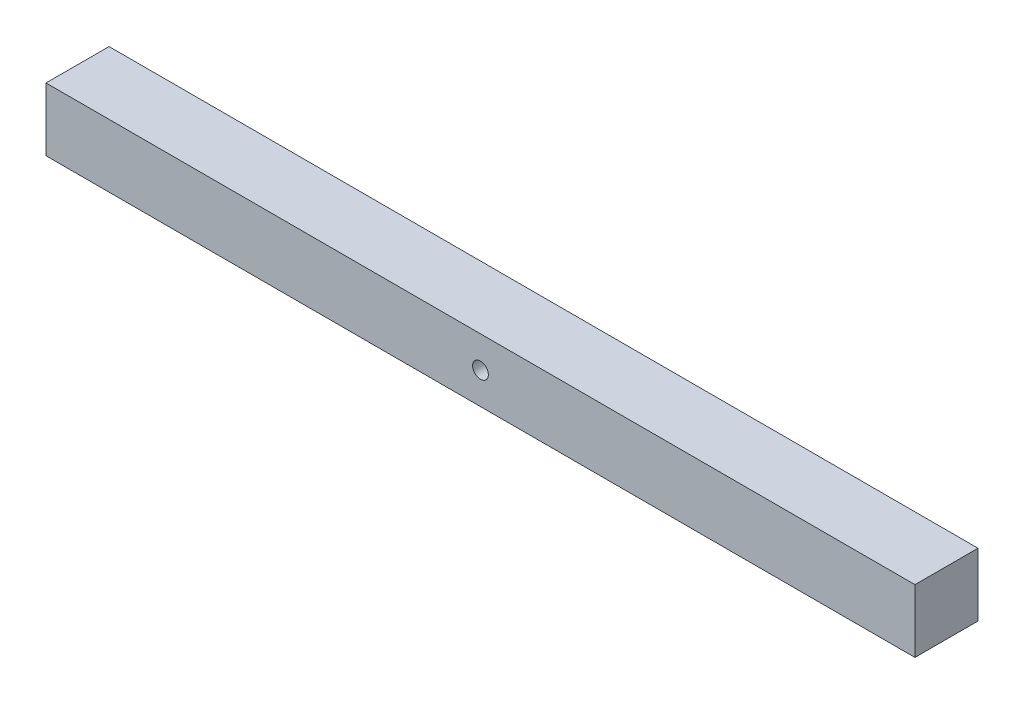
SolidWorks part; units mm, degrees
ref_plane "Front Plane" through (0, 0, 0) normal (0, 0, 1) x (1, 0, 0)
ref_plane "Top Plane" through (0, 0, 0) normal (0, 1, 0) x (1, 0, 0)
ref_plane "Right Plane" through (0, 0, 0) normal (1, 0, 0) x (0, 0, -1)
sketch "Sketch1" plane through (0, 0, 0) normal (0, 0, 1) x (1, 0, 0)
  line L0 (-40.2875, -8.0591) -> (659.7125, -8.0591) construction
  line L1 (-40.2875, 17.3409) -> (659.7125, 17.3409)
  line L2 (-40.2875, 17.3409) -> (-40.2875, -33.4591)
  line L3 (-40.2875, -33.4591) -> (659.7125, -33.4591)
  line L4 (659.7125, 17.3409) -> (659.7125, -33.4591)
  line L5 (309.7125, 17.3409) -> (309.7125, -33.4591) construction
  circle A0 centre (309.7125, -8.0591) radius 6.35
  dimension "D3" = 12.7
  dimension "D1" = 700
  dimension "D2" = 50.8
extrude "Boss-Extrude1" add sketch "Sketch1" along normal blind 50.8
